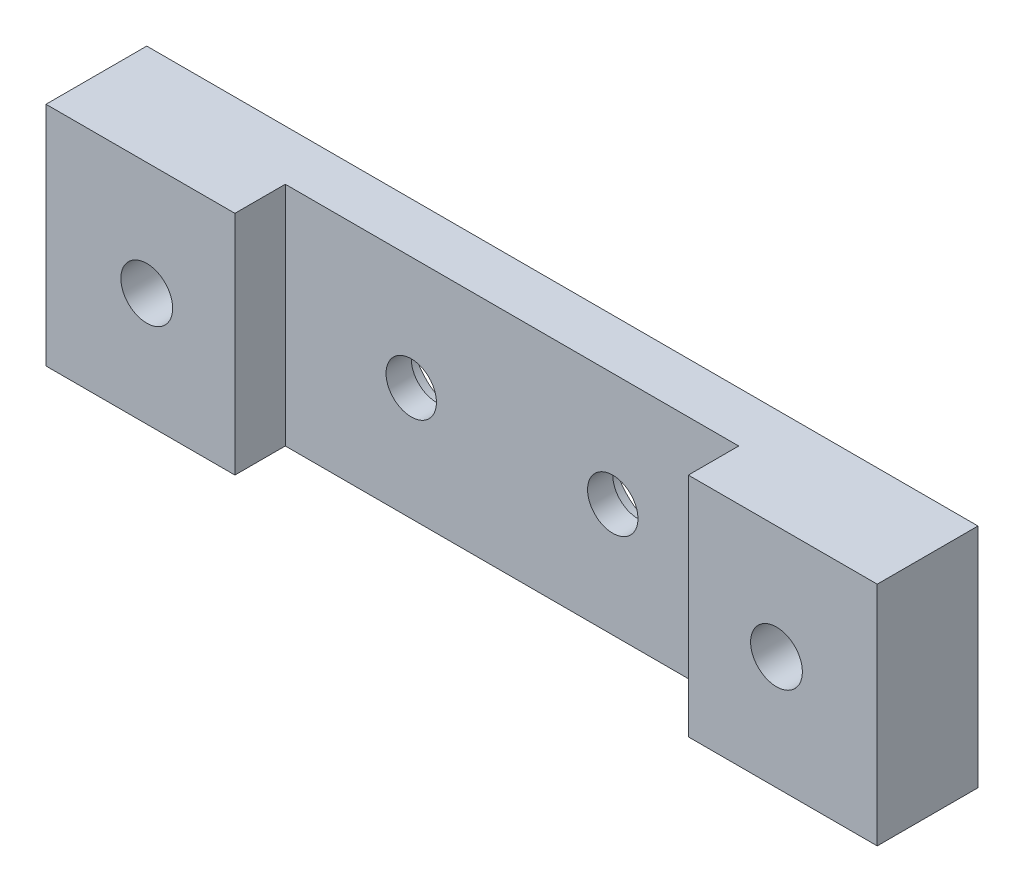
SolidWorks part; units mm, degrees
ref_plane "Front Plane" through (0, 0, 0) normal (0, 0, 1) x (1, 0, 0)
ref_plane "Top Plane" through (0, 0, 0) normal (0, 1, 0) x (1, 0, 0)
ref_plane "Right Plane" through (0, 0, 0) normal (1, 0, 0) x (0, 0, -1)
sketch "Sketch1" plane through (0, 0, 0) normal (0, 1, 0) x (1, 0, 0)
  line L0 (-52.3875, 0) -> (52.3875, 0)
  line L1 (52.3875, 0) -> (52.3875, -12.7)
  line L2 (52.3875, -12.7) -> (28.575, -12.7)
  line L3 (28.575, -12.7) -> (28.575, -6.35)
  line L4 (28.575, -6.35) -> (-28.575, -6.35)
  line L5 (-28.575, -6.35) -> (-28.575, -12.7)
  line L6 (-28.575, -12.7) -> (-52.3875, -12.7)
  line L7 (-52.3875, -12.7) -> (-52.3875, 0)
  point P7 (0, 0)
  point P10 (0, -6.35)
  dimension "D1" = 104.775
  dimension "D2" = 12.7
  dimension "D3" = 57.15
  dimension "D4" = 6.35
extrude "Boss-Extrude1" add sketch "Sketch1" along normal blind 28.575
hole_wizard "Hole1" positions "Sketch2" profile "Sketch3" legacy end condition through all
sketch "Sketch2" plane through (0, 0, 0) normal (0, 0, -1) x (-1, 0, 0)
  line L0 (-12.7, 14.2875) -> (12.7, 14.2875) construction
  line L2 (-52.3875, 28.575) -> (-52.3875, 0) construction
  point P0 (-12.7, 14.2875)
  point P2 (12.7, 14.2875)
  point P13 (0, 14.2875)
  point P18 (-52.3875, 14.2875)
  dimension "D1" = 25.4
sketch "Sketch3" plane through (12.7, 14.2875, 0) normal (1, 0, 0) x (0, 1, 0)
  line L0 (0, 0) -> (0, 14.6077)
  line L1 (0, 14.6077) -> (3.175, 12.7)
  line L2 (3.175, 12.7) -> (3.175, 3.175)
  line L3 (3.175, 3.175) -> (6.35, 3.175)
  line L4 (6.35, 0) -> (0, 0)
  line L5 (0, -11.3109) -> (0, 121.1557) construction
  line L6 (0, 14.6077) -> (-3.175, 12.7) construction
  line L7 (6.35, 3.175) -> (6.35, 0)
  dimension "Depth" = 12.7
  dimension "Drill Angle" = 118
  dimension "Diameter" = 6.35
  dimension "C-Bore Diameter" = 12.7
  dimension "C-Bore Depth" = 3.175
hole_wizard "5/16-18 Tapped Hole1" positions "Sketch6" profile "Sketch5" tap size "5/16-18" standard "ANSI Inch" end condition through all
sketch "Sketch6" plane through (0, 0, 12.7) normal (0, 0, 1) x (1, 0, 0)
  line L0 (-52.3875, 28.575) -> (-52.3875, 0) construction
  line L3 (52.3875, 28.575) -> (52.3875, 0) construction
  line L4 (-28.575, 28.575) -> (28.575, 28.575) construction
  point P0 (-39.6875, 14.2875)
  point P2 (39.6875, 14.2875)
  point P8 (-52.3875, 14.2875)
  point P20 (52.3875, 14.2875)
  point P23 (0, 28.575)
  dimension "D1" = 79.375
  dimension "D2" = 39.6875
sketch "Sketch5" plane through (-39.6875, 14.2875, 12.7) normal (1, 0, 0) x (0, -1, 0)
  line L0 (0, 0) -> (0, 12.7)
  line L1 (0, 12.7) -> (3.2639, 12.7)
  line L2 (3.2639, 12.7) -> (3.2639, 0)
  line L5 (3.2639, 0) -> (0, 0)
  line L11 (0, -6.35) -> (0, 107.95) construction
  dimension "Thru Tap Drill Dia." = 6.5278
  dimension "Thru Tap Drill Depth" = 12.7
cosmetic thread "Hole Thread1" parameters "D2"=7.9375
cosmetic thread "Hole Thread2" parameters "D2"=7.9375
ref_plane "Plane1" through (0, 14.2875, 0) normal (0, 1, 0) x (1, 0, 0)
equation "\"D2@Sketch6\"=\"D1@Sketch6\"/2"
